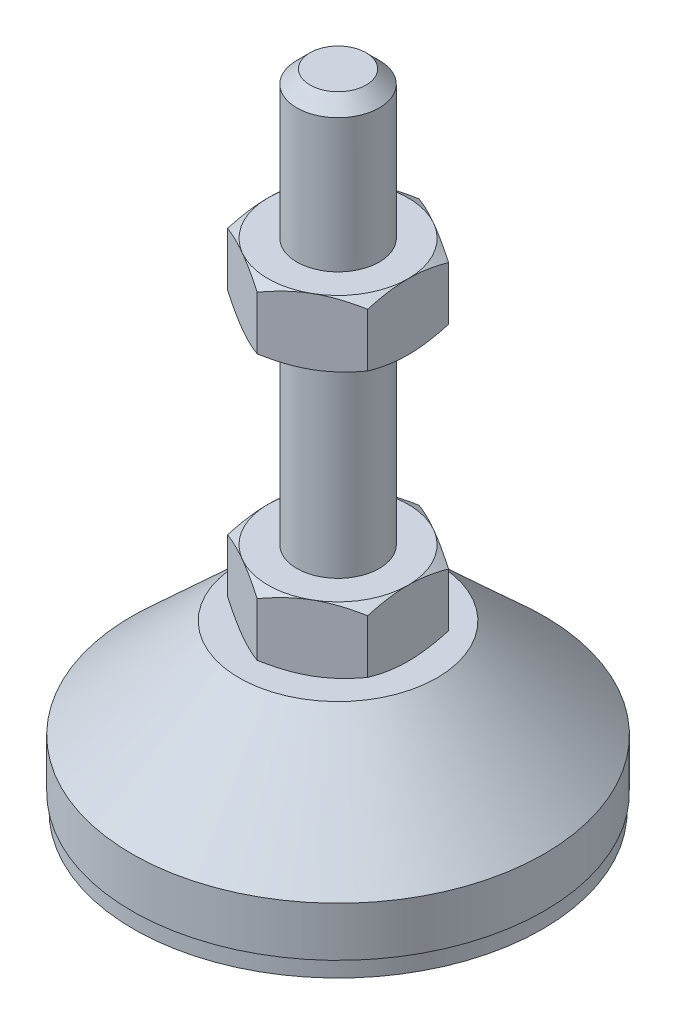
SolidWorks part; units mm, degrees
ref_plane "Спереди" through (0, 0, 0) normal (0, 0, 1) x (1, 0, 0)
ref_plane "Сверху" through (0, 0, 0) normal (0, 1, 0) x (1, 0, 0)
ref_plane "Справа" through (0, 0, 0) normal (1, 0, 0) x (0, 0, -1)
sketch "Эскиз1" plane through (0, 0, 0) normal (0, 0, 1) x (1, 0, 0)
  line L0 (0, 0) -> (-24.8, 0)
  line L1 (-24.8, 0) -> (-24.8, 2)
  line L2 (-24.8, 2) -> (-25, 2)
  line L3 (-25, 2) -> (-25, 8)
  line L4 (-25, 8) -> (-12, 20)
  line L5 (-12, 20) -> (-5, 20)
  line L12 (-5, 28) -> (-5, 76.4)
  line L13 (-5, 76.4) -> (-3.4, 78)
  line L14 (-3.4, 78) -> (0, 78)
  line L15 (0, 78) -> (0, 0) construction
  line L16 (-5, 20) -> (0, 20) construction
  line L17 (0, 0) -> (0, 78)
  line L18 (0, 0) -> (0, -7.9595) construction
  line L19 (-5, 28) -> (-5, 20)
  point P8 (-5, 52.2)
  point P23 (-8.5, 20)
  dimension "D1" = 10
  dimension "D2" = 20
  dimension "D3" = 8
  dimension "D4" = 50
  dimension "D5" = 5
  dimension "D6" = 1.6
  dimension "D7" = 45
  dimension "D8" = 24
  dimension "D9" = 2
  dimension "D10" = 50
  dimension "D11" = 6
  dimension "D12" = 0.2
revolve "Повернуть1" add sketch "Эскиз1" angle 360 about L17
sketch "Эскиз2" plane through (0, 20, 0) normal (0, 1, 0) x (1, 0, 0)
  line L1 (0, 9.815) -> (-8.5, 4.9075)
  line L2 (-8.5, 4.9075) -> (-8.5, -4.9075)
  line L3 (-8.5, -4.9075) -> (0, -9.815)
  line L4 (0, -9.815) -> (8.5, -4.9075)
  line L5 (8.5, -4.9075) -> (8.5, 4.9075)
  line L6 (8.5, 4.9075) -> (0, 9.815)
  circle A0 centre (0, 0) radius 8.5 construction
  dimension "D1" = 17
extrude "Бобышка-Вытянуть1" add sketch "Эскиз2" along normal up to vertex (8 mm away) up to point (-5, 28, 0)
ref_plane "Плоскость1" through (0, 52.2, 0) normal (0, 1, 0) x (1, 0, 0)
sketch "Эскиз3" plane through (0, 52.2, 0) normal (0, 1, 0) x (1, 0, 0)
  line L6 (8.5, 4.9075) -> (0, 9.815)
  line L7 (0, 9.815) -> (-8.5, 4.9075)
  line L8 (-8.5, 4.9075) -> (-8.5, -4.9075)
  line L9 (-8.5, -4.9075) -> (0, -9.815)
  line L10 (0, -9.815) -> (8.5, -4.9075)
  line L11 (8.5, -4.9075) -> (8.5, 4.9075)
  line L12 (8.5, 4.9075) -> (0, 9.815)
  line L13 (0, 9.815) -> (-8.5, 4.9075)
  line L14 (-8.5, 4.9075) -> (-8.5, -4.9075)
  line L15 (-8.5, -4.9075) -> (0, -9.815)
  line L16 (0, -9.815) -> (8.5, -4.9075)
  line L17 (8.5, -4.9075) -> (8.5, 4.9075)
  dimension "D1" = 0
extrude "Бобышка-Вытянуть2" add sketch "Эскиз3" along normal blind 8
sketch "Эскиз4" plane through (0, 0, 0) normal (0, 0, 1) x (1, 0, 0)
  line L0 (-8.5, 60.2) -> (-15.4282, 56.2)
  line L1 (-15.4282, 56.2) -> (-15.4282, 60.2)
  line L2 (-15.4282, 60.2) -> (-8.5, 60.2)
  line L3 (-15.4282, 56.2) -> (-8.5, 52.2)
  line L4 (50, 52.2) -> (-50, 52.2) construction
  line L5 (-8.5, 52.2) -> (-15.4282, 52.2)
  line L6 (-15.4282, 52.2) -> (-15.4282, 56.2)
  line L7 (-8.5, 60.2) -> (-8.5, 52.2) construction
  line L8 (-8.5, 28) -> (-15.4282, 28)
  line L9 (-15.4282, 28) -> (-15.4282, 24)
  line L10 (-15.4282, 24) -> (-8.5, 28)
  line L11 (-8.5, 20) -> (-15.4282, 24)
  line L12 (-15.4282, 24) -> (-15.4282, 20)
  line L13 (-15.4282, 20) -> (-8.5, 20)
  line L14 (0, 78) -> (0, 96.3793) construction
  dimension "D1" = 30
  dimension "D2" = 30
revolve "Вырез-Повернуть2" cut sketch "Эскиз4" angle 360 about L14
